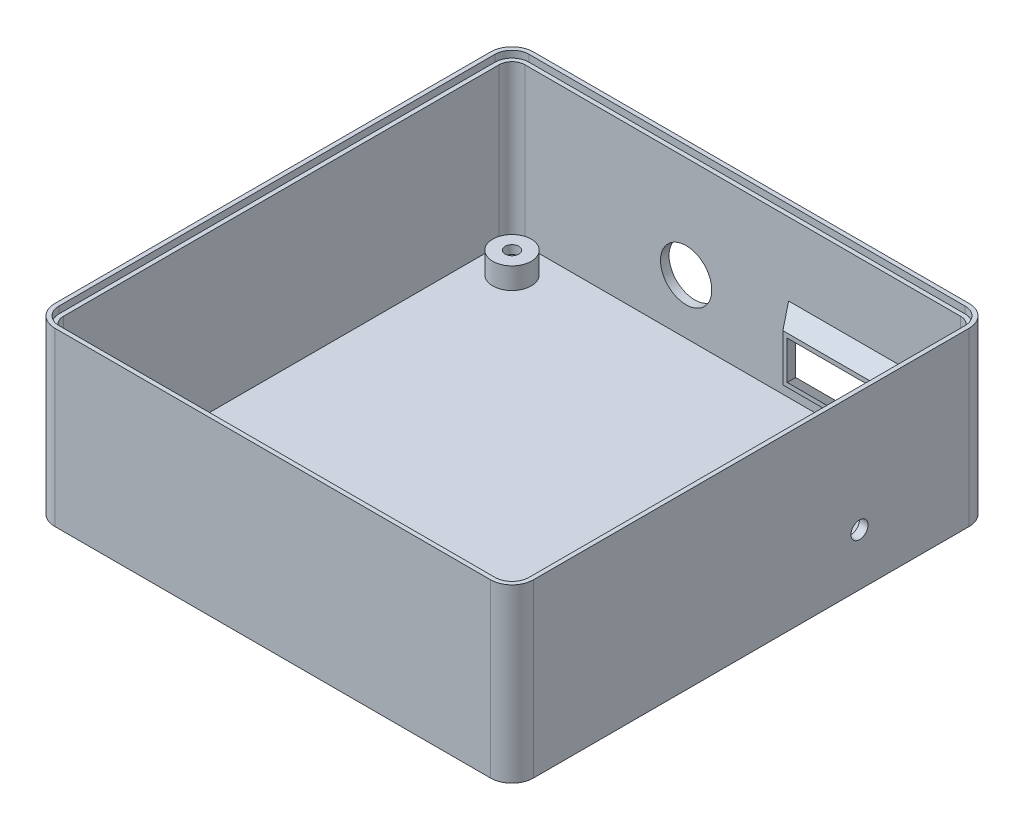
SolidWorks part; units mm, degrees
ref_plane "Front Plane" through (0, 0, 0) normal (0, 0, 1) x (1, 0, 0)
ref_plane "Top Plane" through (0, 0, 0) normal (0, 1, 0) x (1, 0, 0)
ref_plane "Right Plane" through (0, 0, 0) normal (1, 0, 0) x (0, 0, -1)
sketch "Sketch1" plane through (0, 0, 0) normal (0, 1, 0) x (1, 0, 0)
  line L1 (-51, -56) -> (51, -56)
  line L2 (-56, -51) -> (-56, 51)
  line L3 (-51, 56) -> (51, 56)
  line L4 (56, -51) -> (56, 51)
  line L5 (-56, -56) -> (56, 56) construction
  line L6 (-56, 56) -> (56, -56) construction
  arc A0 (-51, -56) -> (-56, -51) centre (-51, -51) cw
  arc A1 (51, -56) -> (56, -51) centre (51, -51) ccw
  arc A2 (51, 56) -> (56, 51) centre (51, 51) cw
  arc A3 (-56, 51) -> (-51, 56) centre (-51, 51) cw
  point P0 (0, 0)
  dimension "D2" = 5
  dimension "D1" = 112
  dimension "D3" = 112
extrude "Boss-Extrude1" add sketch "Sketch1" along normal blind 40.2
sketch "Sketch3" plane through (0, 40.2, 0) normal (0, 1, 0) x (1, 0, 0)
  line L8 (-51, -55) -> (51, -55)
  line L9 (55, -51) -> (55, 51)
  line L10 (51, 55) -> (-51, 55)
  line L11 (-55, 51) -> (-55, -51)
  line L12 (-51, -55) -> (51, -55)
  line L13 (55, -51) -> (55, 51)
  line L14 (51, 55) -> (-51, 55)
  line L15 (-55, 51) -> (-55, -51)
  arc A8 (-55, -51) -> (-51, -55) centre (-51, -51) ccw
  arc A9 (51, -55) -> (55, -51) centre (51, -51) ccw
  arc A10 (55, 51) -> (51, 55) centre (51, 51) ccw
  arc A11 (-51, 55) -> (-55, 51) centre (-51, 51) ccw
  arc A12 (-55, -51) -> (-51, -55) centre (-51, -51) ccw
  arc A13 (51, -55) -> (55, -51) centre (51, -51) ccw
  arc A14 (55, 51) -> (51, 55) centre (51, 51) ccw
  arc A15 (-51, 55) -> (-55, 51) centre (-51, 51) ccw
  dimension "D1" = 1
extrude "Cut-Extrude1" cut sketch "Sketch3" against normal blind 1.6
sketch "Sketch4" plane through (0, 38.6, 0) normal (0, 1, 0) x (1, 0, 0)
  line L8 (-51, -54) -> (51, -54)
  line L9 (54, -51) -> (54, 51)
  line L10 (51, 54) -> (-51, 54)
  line L11 (-54, 51) -> (-54, -51)
  line L12 (-51, -54) -> (51, -54)
  line L13 (54, -51) -> (54, 51)
  line L14 (51, 54) -> (-51, 54)
  line L15 (-54, 51) -> (-54, -51)
  arc A8 (-54, -51) -> (-51, -54) centre (-51, -51) ccw
  arc A9 (51, -54) -> (54, -51) centre (51, -51) ccw
  arc A10 (54, 51) -> (51, 54) centre (51, 51) ccw
  arc A11 (-51, 54) -> (-54, 51) centre (-51, 51) ccw
  arc A12 (-54, -51) -> (-51, -54) centre (-51, -51) ccw
  arc A13 (51, -54) -> (54, -51) centre (51, -51) ccw
  arc A14 (54, 51) -> (51, 54) centre (51, 51) ccw
  arc A15 (-51, 54) -> (-54, 51) centre (-51, 51) ccw
  dimension "D1" = 1
extrude "Cut-Extrude2" cut sketch "Sketch4" against normal blind 36.6
sketch "Sketch5" plane through (0, 0, 0) normal (0, -1, 0) x (1, 0, 0)
  line L0 (-56, 0) -> (56, 0) construction
  line L1 (56, 51) -> (56, -51) construction
  line L2 (0, -56) -> (0, 56) construction
  line L3 (-51, 56) -> (51, 56) construction
  point P6 (0, 0)
  point P12 (0, 0)
sketch "Sketch6" plane through (0, 2, 0) normal (0, 1, 0) x (1, 0, 0)
  line L0 (51, 55) -> (-51, 55) construction
  line L1 (-55, 51) -> (-55, -51) construction
  circle A0 centre (-46.5, 46.5) radius 4.5
  dimension "D3" = 9
  dimension "D1" = 8.5
  dimension "D2" = 8.5
extrude "Boss-Extrude2" add sketch "Sketch6" along normal blind 5
sketch "Sketch10" plane through (0, 7, 0) normal (0, 1, 0) x (1, 0, 0)
  circle A0 centre (-46.5, 46.5) radius 1.6
  dimension "D1" = 3.2
extrude "Cut-Extrude4" cut sketch "Sketch10" along normal through all both and the other way through all
sketch "Sketch11" plane through (0, 0, 0) normal (0, -1, 0) x (1, 0, 0)
  circle A0 centre (-46.5, -46.5) radius 3.5
  dimension "D1" = 7
extrude "Cut-Extrude6" cut sketch "Sketch11" against normal blind 5
pattern_linear "LPattern1" count 2 spacing 93 along (0, 0, 1) count 2 spacing 93 along (1, 0, 0) of "Boss-Extrude2", "Cut-Extrude6", "Cut-Extrude4"
sketch "Sketch15" plane through (0, 0, -56) normal (0, 0, -1) x (-1, 0, 0)
  line L1 (-39.76, 3.9) -> (-9.4, 3.9)
  line L2 (-39.76, 3.9) -> (-39.76, 22.9)
  line L3 (-39.76, 22.9) -> (-9.4, 22.9)
  line L4 (-9.4, 3.9) -> (-9.4, 22.9)
  line L5 (-39.76, 3.9) -> (-9.4, 22.9) construction
  line L6 (-39.76, 22.9) -> (-9.4, 3.9) construction
  line L8 (56, 0) -> (-56, 0) construction
  line L9 (-51, 40.2) -> (-51, 0) construction
  point P0 (-24.58, 13.4)
  dimension "D1" = 30.36
  dimension "D2" = 19
  dimension "D3" = 13.4
  dimension "D4" = 26.42
ref_plane "Plane1" through (0, 0, -50) normal (0, 0, 1) x (1, 0, 0)
sketch "Sketch17" plane through (0, 0, -50) normal (0, 0, 1) x (1, 0, 0)
  line L1 (35.76, 7.9) -> (13.4, 7.9)
  line L2 (35.76, 7.9) -> (35.76, 18.9)
  line L3 (35.76, 18.9) -> (13.4, 18.9)
  line L4 (13.4, 7.9) -> (13.4, 18.9)
  line L5 (35.76, 7.9) -> (13.4, 18.9) construction
  line L6 (35.76, 18.9) -> (13.4, 7.9) construction
  point P0 (24.58, 13.4)
  dimension "D1" = 22.36
  dimension "D2" = 11
loft "Loft1" add profiles "Sketch15", "Sketch17"
sketch "Sketch18" plane through (0, 0, -50) normal (0, 0, 1) x (1, 0, 0)
  line L1 (14.4, 8.9) -> (34.76, 8.9)
  line L2 (14.4, 8.9) -> (14.4, 17.9)
  line L3 (14.4, 17.9) -> (34.76, 17.9)
  line L4 (34.76, 8.9) -> (34.76, 17.9)
  line L5 (14.4, 8.9) -> (34.76, 17.9) construction
  line L6 (14.4, 17.9) -> (34.76, 8.9) construction
  point P0 (24.58, 13.4)
  dimension "D1" = 20.36
  dimension "D2" = 9
sketch "Sketch19" plane through (0, 0, -56) normal (0, 0, -1) x (-1, 0, 0)
  line L1 (-38.76, 4.9) -> (-10.4, 4.9)
  line L2 (-38.76, 4.9) -> (-38.76, 21.9)
  line L3 (-38.76, 21.9) -> (-10.4, 21.9)
  line L4 (-10.4, 4.9) -> (-10.4, 21.9)
  line L5 (-38.76, 4.9) -> (-10.4, 21.9) construction
  line L6 (-38.76, 21.9) -> (-10.4, 4.9) construction
  point P0 (-24.58, 13.4)
  dimension "D1" = 28.36
  dimension "D2" = 17
loft "Cut-Loft2" cut profiles "Sketch19", "Sketch18"
sketch "Sketch21" plane through (56, 0.2229, 12.4896) normal (1, 0, 0) x (0, 0, -1)
  line L0 (-38.5104, -0.2229) -> (63.4896, -0.2229) construction
  line L1 (62.4896, 19.9071) -> (62.4896, -20.3529) construction
  circle A0 centre (37.8081, 11.9562) radius 2
  dimension "D1" = 4
  dimension "D2" = 12.1791
  dimension "D3" = 24.6815
extrude "Cut-Extrude7" cut sketch "Sketch21" against normal up to next
sketch "Sketch22" plane through (0, 0, -56) normal (0, 0, -1) x (-1, 0, 0)
  line L0 (-10.4, 4.9) -> (-10.4, 21.9) construction
  circle A0 centre (13.2462, 14.8095) radius 6
  dimension "D1" = 12
  dimension "D2" = 23.6462
extrude "Cut-Extrude8" cut sketch "Sketch22" against normal up to next
